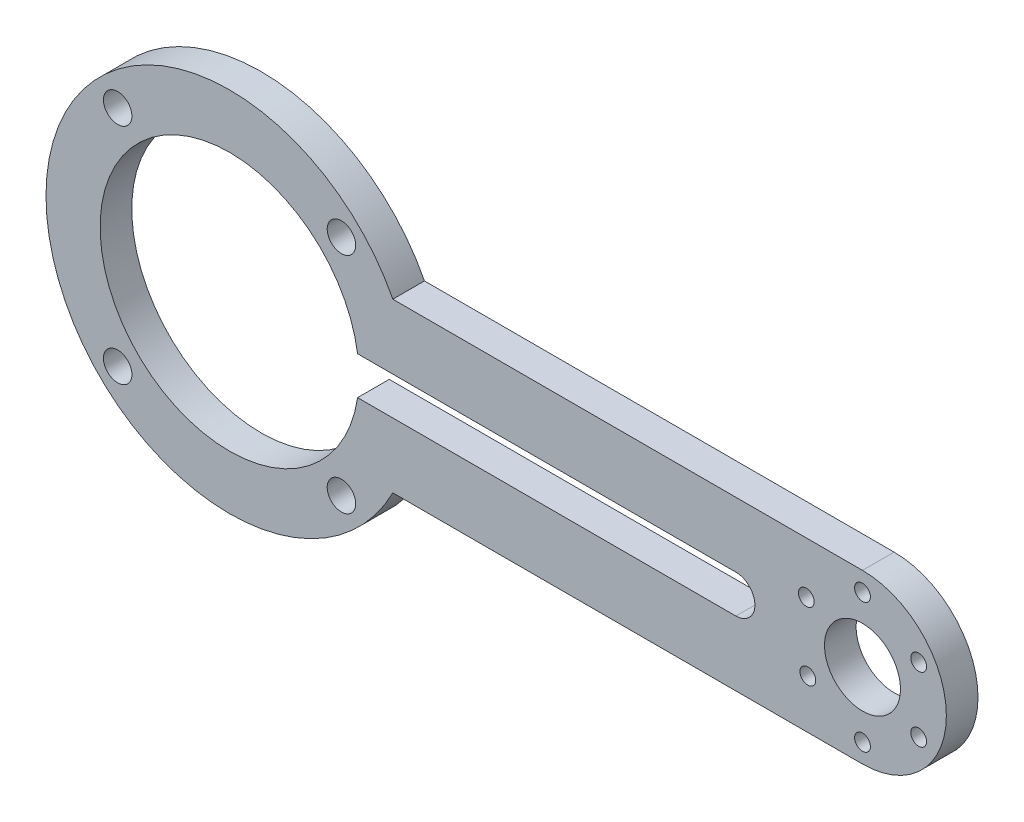
SolidWorks part; units mm, degrees
material "Wrought Stainless Steel"
ref_plane "Front Plane" through (0, 0, 0) normal (0, 0, 1) x (1, 0, 0)
ref_plane "Top Plane" through (0, 0, 0) normal (0, 1, 0) x (1, 0, 0)
ref_plane "Right Plane" through (0, 0, 0) normal (1, 0, 0) x (0, 0, -1)
sketch "Sketch2" plane through (0, 0, 0) normal (0, 0, 1) x (1, 0, 0)
  line L0 (0, 13.25) -> (100, 13.25)
  line L1 (0, -13.25) -> (100, -13.25)
  line L2 (50, 0) -> (50, -3)
  line L3 (50, 0) -> (50, 3)
  line L4 (20, 3) -> (80, 3)
  line L5 (20, -3) -> (80, -3)
  circle A0 centre (0, 0) radius 29
  circle A1 centre (0, 0) radius 20.45
  circle A2 centre (0, 0) radius 13.25
  circle A3 centre (100, 0) radius 13.25
  circle A4 centre (80, 0) radius 3
  circle A5 centre (20, 0) radius 3
  circle A6 centre (100, 0) radius 6
  point P18 (50, 3)
  point P20 (50, -3)
extrude "Boss-Extrude1" add sketch "Sketch2" along normal blind 5 contours A1 L0 A0 L1 | A1 L1 A0 L5 | A1 L4 A0 L0 | A4 L5 A0 L1 A3 L0 L4 | A3 A6
sketch "Sketch3" plane through (0, 0, 5) normal (0, 0, 1) x (1, 0, 0)
  line L0 (0, 0) -> (17.6777, 17.6777)
  line L1 (0, 0) -> (17.6777, -17.6777)
  line L2 (0, 0) -> (-17.6777, -17.6777)
  line L3 (0, 0) -> (-17.6777, 17.6777)
  line L4 (100, 0) -> (108.8768, 5.125)
  line L5 (100, 0) -> (108.8768, -5.125)
  line L6 (100, 0) -> (100, -10.25)
  line L7 (100, 0) -> (91.1232, -5.125)
  line L8 (100, 0) -> (91.1232, 5.125)
  circle A0 centre (0, 0) radius 25
  circle A1 centre (17.6777, 17.6777) radius 2.25
  circle A2 centre (17.6777, -17.6777) radius 2.25
  circle A3 centre (-17.6777, -17.6777) radius 2.25
  circle A4 centre (-17.6777, 17.6777) radius 2.25
  circle A5 centre (100, 0) radius 10.25
  circle A6 centre (100, 10.25) radius 1.25
  circle A7 centre (108.8768, 5.125) radius 1.25
  circle A8 centre (91.1232, 5.125) radius 1.25
  circle A9 centre (91.3623, -5.5184) radius 1.25
  circle A10 centre (108.8768, -5.125) radius 1.25
  circle A11 centre (100, -10.25) radius 1.25
extrude "Cut-Extrude1" cut sketch "Sketch3" against normal through all contours A8 | A6 | A7 | A10 | A11 | A9 | A1 | A2 | A3 | A4
